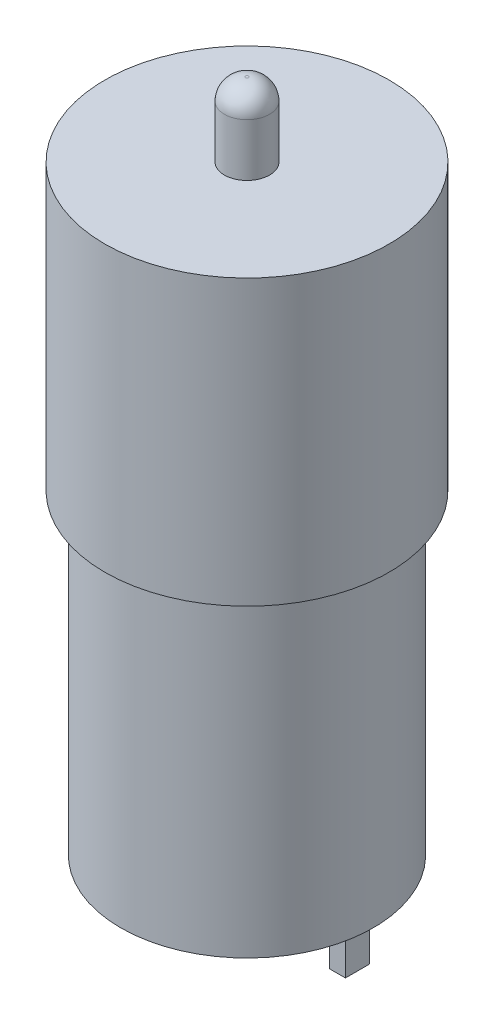
SolidWorks part; units mm, degrees
ref_plane "Front Plane" through (0, 0, 0) normal (0, 0, 1) x (1, 0, 0)
ref_plane "Top Plane" through (0, 0, 0) normal (0, 1, 0) x (1, 0, 0)
ref_plane "Right Plane" through (0, 0, 0) normal (1, 0, 0) x (0, 0, -1)
sketch "Sketch1" plane through (0, 0, 0) normal (0, 1, 0) x (1, 0, 0)
  circle A0 centre (0, 0) radius 12
  dimension "D1" = 24
extrude "Boss-Extrude1" add sketch "Sketch1" along normal blind 30
sketch "Sketch2" plane through (0, 30, 0) normal (0, 1, 0) x (1, 0, 0)
  circle A0 centre (0, 0) radius 13.5
extrude "Boss-Extrude2" add sketch "Sketch2" along normal blind 27
sketch "Sketch3" plane through (0, 57, 0) normal (0, 1, 0) x (1, 0, 0)
  circle A0 centre (0, 0) radius 2.15
extrude "Boss-Extrude3" add sketch "Sketch3" along normal blind 7
fillet "Fillet1" radius 2 1 edges at (0, 64, 2.15)
sketch "Sketch4" plane through (0, 0, 0) normal (0, -1, 0) x (1, 0, 0)
  circle A0 centre (0, 0) radius 3.215
  dimension "D1" = 6.43
extrude "Boss-Extrude4" add sketch "Sketch4" along normal blind 2.32
fillet "Fillet2" radius 2 1 edges at (0, -2.32, -3.215)
sketch "Sketch5" plane through (0, 0, 0) normal (0, -1, 0) x (1, 0, 0)
  line L0 (12, 0) -> (-12, 0) construction
  line L1 (0, -12) -> (0, 12) construction
  line L2 (9, 1.15) -> (10.5, 1.15)
  line L3 (9, 1.15) -> (9, -1.15)
  line L4 (9, -1.15) -> (10.5, -1.15)
  line L5 (10.5, 1.15) -> (10.5, -1.15)
  line L6 (9, 1.15) -> (10.5, -1.15) construction
  line L7 (9, -1.15) -> (10.5, 1.15) construction
  line L8 (-9, -1.15) -> (-10.5, 1.15) construction
  line L9 (-9, 1.15) -> (-10.5, -1.15) construction
  line L10 (-10.5, 1.15) -> (-10.5, -1.15)
  line L11 (-9, -1.15) -> (-10.5, -1.15)
  line L12 (-9, 1.15) -> (-9, -1.15)
  line L13 (-9, 1.15) -> (-10.5, 1.15)
  circle A0 centre (0, 0) radius 12 construction
  point P5 (9.75, 0)
  point P16 (-9.75, 0)
  dimension "D1" = 1.5
  dimension "D2" = 1.15
  dimension "D3" = 1.5
extrude "Boss-Extrude5" add sketch "Sketch5" along normal blind 4.3
